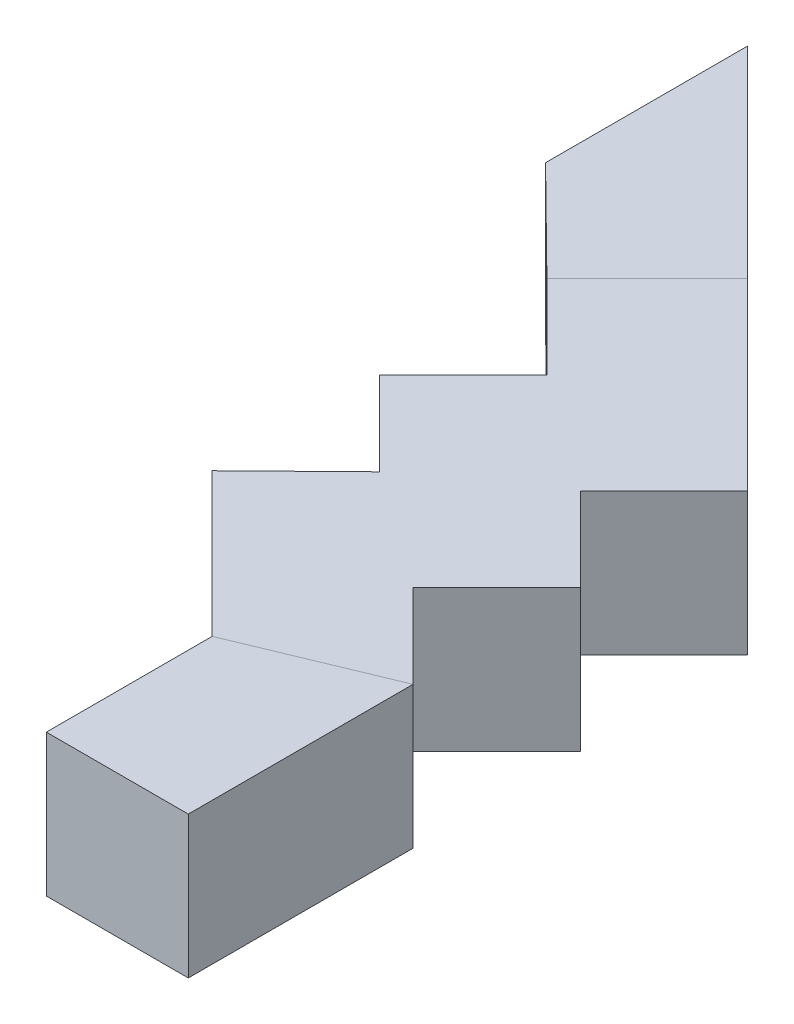
SolidWorks part; units mm, degrees
ref_plane "Front Plane" through (0, 0, 0) normal (0, 0, 1) x (1, 0, 0)
ref_plane "Top Plane" through (0, 0, 0) normal (0, 1, 0) x (1, 0, 0)
ref_plane "Right Plane" through (0, 0, 0) normal (1, 0, 0) x (0, 0, -1)
sketch "Sketch1" plane through (0, 0, 0) normal (0, 1, 0) x (1, 0, 0)
  line L0 (0, 0) -> (-1000, 0)
  line L1 (0, 0) -> (0, 600)
  line L2 (0, 600) -> (-1000, 600)
  line L3 (-1000, 0) -> (-2062.5184, -284.7009)
  line L4 (-2062.5184, -284.7009) -> (-3015.1464, -834.7009)
  line L5 (-1155.2914, 579.5555) -> (-2217.8098, 294.8545)
  line L6 (-1000, 600) -> (-1155.2914, 579.5555)
  line L7 (-3015.1464, -834.7009) -> (-3792.9638, -1612.5184)
  line L8 (-2217.8098, 294.8545) -> (-2362.5184, 234.9143)
  line L9 (-2362.5184, 234.9143) -> (-3315.1464, -315.0857)
  line L11 (-3439.4104, -410.4369) -> (-4217.2279, -1188.2543)
  line L12 (-3315.1464, -315.0857) -> (-3439.4104, -410.4369)
  line L26 (-8010.1917, -2800.7727) -> (-7010.1917, -2800.7727)
  line L27 (-8010.1917, -2800.7727) -> (-8010.1917, -3400.7727)
  line L28 (-8010.1917, -3400.7727) -> (-7010.1917, -3400.7727)
  line L29 (-7010.1917, -2800.7727) -> (-5947.6733, -2516.0718)
  line L30 (-5947.6733, -2516.0718) -> (-4995.0453, -1966.0718)
  line L31 (-6854.9003, -3380.3282) -> (-5792.3819, -3095.6273)
  line L32 (-7010.1917, -3400.7727) -> (-6854.9003, -3380.3282)
  line L33 (-4995.0453, -1966.0718) -> (-4217.2279, -1188.2543)
  line L34 (-5792.3819, -3095.6273) -> (-5647.6733, -3035.687)
  line L35 (-5647.6733, -3035.687) -> (-4695.0453, -2485.687)
  line L36 (-4570.7813, -2390.3359) -> (-3792.9638, -1612.5184)
  line L37 (-4695.0453, -2485.687) -> (-4570.7813, -2390.3359)
extrude "Boss-Extrude1" add sketch "Sketch1" against normal blind 600
sketch "Sketch7" plane through (0, 0, 0) normal (0, 0, 1) x (1, 0, 0)
  line L0 (-3015.1464, -400) -> (-3015.1464, 0)
  line L1 (-2062.5184, -600) -> (-2062.5184, 0) construction
  line L2 (-3015.1464, -400) -> (-2062.5184, -400)
  line L3 (-3015.1464, -600) -> (-3015.1464, 0) construction
  line L4 (-1000, -600) -> (-1000, 0)
  line L5 (-2062.5184, -400) -> (-1000, -600)
extrude "Cut-Extrude9" cut sketch "Sketch7" against normal through all and the other way through all
sketch "Sketch8" plane through (0, 0, 0) normal (0, 0, 1) x (1, 0, 0)
  line L0 (-1000, -600) -> (0, -600)
  line L1 (0, -600) -> (0, 0)
  line L2 (-1000, -600) -> (-1000, 0)
  line L5 (-4570.7813, -600) -> (-4570.7813, 0) construction
  line L6 (-4570.7813, -200) -> (-3015.1464, -400)
  line L7 (-4570.7813, -200) -> (-4695.0453, -200)
  line L8 (-4695.0453, -600) -> (-4695.0453, 0) construction
  line L9 (-4695.0453, -200) -> (-4695.0453, 0)
extrude "Cut-Extrude-Thin1" cut sketch "Sketch8" against normal through all thin thin type one direction wall 10
sketch "Sketch9" plane through (-1090.2227, 0, -1090.2227) normal (0.7071, 0, 0.7071) x (0.7071, 0, -0.7071)
  line L0 (-4922.2531, 0) -> (-4922.2531, -200)
  line L1 (-4922.2531, -600) -> (-4922.2531, 0) construction
  line L3 (-2722.2531, -400) -> (-2722.2531, 0)
  line L4 (-2722.2531, -400) -> (-2722.2531, 0) construction
sketch "Sketch14" plane through (0, -400, 0) normal (0, 1, 0) x (1, 0, 0)
  line L0 (-3015.1464, -834.7009) -> (-3439.4104, -410.4369)
  line L1 (-3015.1464, -834.7009) -> (-3015.1464, -141.8806)
  line L2 (-3015.1464, -834.7009) -> (-3015.1464, -141.8806) construction
  line L3 (-3015.1464, -834.7009) -> (-3015.1464, -141.8806) construction
  line L4 (-3315.1464, -315.0857) -> (-3015.1464, -141.8806)
  line L5 (-3439.4104, -410.4369) -> (-3315.1464, -315.0857)
extrude "Cut-Extrude40" cut sketch "Sketch14" along normal blind 400
sketch "Sketch17" plane through (-1090.2227, 0, -1090.2227) normal (0.7071, 0, 0.7071) x (0.7071, 0, -0.7071)
  line L0 (-2722.2531, -400) -> (-2722.2531, 0)
  line L1 (-4922.2531, -600) -> (-4922.2531, 0) construction
  line L2 (-2722.2531, -400) -> (-4922.2531, -200)
  line L3 (-4922.2531, -200) -> (-4922.2531, 0)
extrude "Cut-Extrude42" cut sketch "Sketch17" along normal through all and the other way through all flip side to cut
sketch "Sketch18" plane through (0, 0, 0) normal (0, 1, 0) x (1, 0, 0)
  line L0 (-4570.7813, -2390.3359) -> (-4995.0453, -1966.0718)
  line L1 (-4995.0453, -1966.0718) -> (-5947.6733, -2516.0718)
  line L2 (-5947.6733, -2516.0718) -> (-5792.3819, -3095.6273)
  line L3 (-5792.3819, -3095.6273) -> (-5647.6733, -3035.687) construction
  line L4 (-6854.9003, -3380.3282) -> (-5792.3819, -3095.6273) construction
  line L5 (-5792.3819, -3095.6273) -> (-5647.6733, -3035.687)
  line L6 (-5647.6733, -3035.687) -> (-4695.0453, -2485.687)
  line L7 (-4695.0453, -2485.687) -> (-4570.7813, -2390.3359)
extrude "Cut-Extrude43" cut sketch "Sketch18" against normal blind 200
sketch "Sketch19" plane through (385.8908, 0, 1440.1641) normal (0.2588, 0, 0.9659) x (0.9659, 0, -0.2588)
  line L0 (-6396.2185, -200) -> (-7496.2185, 0)
  line L1 (-6396.2185, -200) -> (-6396.2185, 0)
extrude "Cut-Extrude44" cut sketch "Sketch19" against normal through all and the other way through all
sketch "Sketch20" plane through (0, 0, 0) normal (0, 1, 0) x (1, 0, 0)
  line L0 (-7010.1917, -3400.7727) -> (-7010.1917, -2800.7727)
  line L1 (-7010.1917, -2800.7727) -> (-8010.1917, -2800.7727)
  line L2 (-7010.1917, -2800.7727) -> (-8010.1917, -2800.7727) construction
  line L3 (-8010.1917, -2800.7727) -> (-8010.1917, -3400.7727)
  line L4 (-8010.1917, -3400.7727) -> (-7010.1917, -3400.7727)
extrude "Cut-Extrude45" cut sketch "Sketch20" against normal blind 600
sketch "Sketch21" plane through (0, 0, 0) normal (0, 1, 0) x (1, 0, 0)
  line L0 (0, 0) -> (-10, 600)
  line L1 (-10, 600) -> (-990, 600)
  line L2 (-990, 600) -> (-1000, 0)
  line L4 (-1000, 0) -> (0, 0)
extrude "Cut-Extrude46" cut sketch "Sketch21" against normal blind 600
sketch "Sketch22" plane through (0, 0, 0) normal (0, 1, 0) x (1, 0, 0)
  line L0 (-7010.1917, -3400.7727) -> (-7610.1917, -3400.7727)
  line L1 (-7010.1917, -3400.7727) -> (-7010.1917, -2800.7727)
  line L2 (-7010.1917, -2800.7727) -> (-7010.1917, -1850.7727)
  line L3 (-7610.1917, -3400.7727) -> (-7610.1917, -2099.7727)
  line L4 (-7610.1917, -2099.7727) -> (-7010.1917, -1850.7727)
extrude "Boss-Extrude2" add sketch "Sketch22" against normal blind 600
sketch "Sketch23" plane through (0, 0, 0) normal (0, 1, 0) x (1, 0, 0)
  line L0 (-7010.1917, -1850.7727) -> (-7363.7451, -1497.2194)
  line L3 (-7610.1917, -2099.7727) -> (-8216.4721, -1493.4923)
  line L4 (-8216.4721, -1493.4923) -> (-7858.7198, -1143.666)
  line L5 (-7858.7198, -1143.666) -> (-8212.2732, -790.1126)
  line L6 (-7363.7451, -1497.2194) -> (-7010.1917, -1143.666)
  line L7 (-7010.1917, -1143.666) -> (-7363.7451, -790.1126)
  line L10 (-7858.7198, -436.5592) -> (-8212.2732, -790.1126)
  line L11 (-7858.7198, -436.5592) -> (-8212.2732, -83.0058)
  line L12 (-7363.7451, -790.1126) -> (-7010.1917, -436.5592)
  line L13 (-7010.1917, -436.5592) -> (-7369.5272, -77.2237)
  line L14 (-7369.5272, -77.2237) -> (-7793.7913, 347.0404)
  line L15 (-7858.7198, 270.5476) -> (-7793.7913, 347.0404)
  line L16 (-8212.2732, -83.0058) -> (-7858.7198, 270.5476)
  line L17 (-7610.1917, -2099.7727) -> (-7010.1917, -1850.7727)
extrude "Boss-Extrude3" add sketch "Sketch23" against normal blind 600
sketch "Sketch24" plane through (0, 0, 0) normal (0, 1, 0) x (1, 0, 0)
  line L0 (-7793.7913, 347.0404) -> (-8639.4431, 1192.6922)
  line L1 (-8212.2732, -83.0058) -> (-8639.4431, 338.3624)
  line L2 (-8639.4431, 338.3624) -> (-8639.4431, 1192.6922)
  line L3 (-8212.2732, -83.0058) -> (-7793.7913, 347.0404)
  line L4 (-8212.2732, -83.0058) -> (-7793.7913, 347.0404)
  dimension "D1" = 45
extrude "Boss-Extrude4" add sketch "Sketch24" against normal blind 600 separate body contours L1 L3 L0 L2
sketch "Sketch27" plane through (-4176.5499, 0, -4064.2397) normal (0.7167, 0, 0.6974) x (0.6974, 0, -0.7167)
  line L1 (-5786.77, 0) -> (-5186.7143, 0)
  line L2 (-5786.77, 0) -> (-5786.77, -600)
  line L3 (-5786.77, -600) -> (-5186.7143, -600)
  line L4 (-5186.7143, 0) -> (-5186.7143, -600)
extrude "Boss-Extrude5" add sketch "Sketch27" along normal up to next
sketch "Sketch29" plane through (0, 0, 0) normal (0, 1, 0) x (1, 0, 0)
  line L0 (-7610.1917, -2099.7727) -> (-7010.1917, -1850.7727)
  line L1 (-8212.2732, -83.0058) -> (-7788.0092, 341.2583)
  line L2 (-7010.1917, -436.5592) -> (-8639.4431, 1192.6922) construction
  line L3 (-8212.2732, -83.0058) -> (-7858.7198, -436.5592)
  line L4 (-7858.7198, -436.5592) -> (-8212.2732, -790.1126)
  line L5 (-8212.2732, -790.1126) -> (-7858.7198, -1143.666)
  line L6 (-7858.7198, -1143.666) -> (-8216.4721, -1493.4923)
  line L7 (-8216.4721, -1493.4923) -> (-7610.1917, -2099.7727)
  line L8 (-7010.1917, -1850.7727) -> (-7363.7451, -1497.2194)
  line L9 (-7363.7451, -1497.2194) -> (-7010.1917, -1143.666)
  line L10 (-7010.1917, -1143.666) -> (-7363.7451, -790.1126)
  line L11 (-7363.7451, -790.1126) -> (-7010.1917, -436.5592)
  line L12 (-7363.7451, -790.1126) -> (-7010.1917, -436.5592) construction
  line L13 (-7010.1917, -436.5592) -> (-7788.0092, 341.2583)
split line "Split Line1"
sketch "Sketch30" plane through (-3723.3754, 0, 3723.3754) normal (0.7071, 0, -0.7071) x (-0.7071, 0, -0.7071)
  line L0 (5748.2601, 0) -> (5748.2601, -600)
  line L1 (4648.2601, -600) -> (6952.3696, -600) construction
split line "Split Line2"
sketch "Sketch31" plane through (-222.2787, 0, -829.5555) normal (-0.2588, 0, -0.9659) x (-0.9659, 0, 0.2588)
  line L0 (1905.1563, -400) -> (1905.1563, -600)
  line L1 (965.9258, -600) -> (2065.9258, -600) construction
split line "Split Line3"
sketch "Sketch39" plane through (0, 0, 0) normal (0, 1, 0) x (1, 0, 0)
  line L0 (-7010.1917, -2800.7727) -> (-7610.1917, -2800.7727)
  line L1 (-7610.1917, -2099.7727) -> (-7610.1917, -3400.7727) construction
ref_plane "Plane2" through (-7010.1917, 0, 0) normal (1, 0, 0) x (0, 0, -1)
sketch "Sketch41" plane through (-7010.1917, 0, 0) normal (1, 0, 0) x (0, 0, -1)
  line L1 (-4395.6011, 900.6876) -> (1548.9916, 900.6876)
  line L2 (-4395.6011, 900.6876) -> (-4395.6011, -944.9527)
  line L3 (-4395.6011, -944.9527) -> (1548.9916, -944.9527)
  line L4 (1548.9916, 900.6876) -> (1548.9916, -944.9527)
extrude "Cut-Extrude49" cut sketch "Sketch41" along normal blind 10020
ref_plane "Plane3" through (0, 0, 2800.7727) normal (0, 0, 1) x (1, 0, 0)
sketch "Sketch42" plane through (0, 0, 2800.7727) normal (0, 0, 1) x (1, 0, 0)
  line L1 (-6414.9989, 710.8912) -> (-9646.0999, 710.8912)
  line L2 (-6414.9989, 710.8912) -> (-6414.9989, -1532.537)
  line L3 (-6414.9989, -1532.537) -> (-9646.0999, -1532.537)
  line L4 (-9646.0999, 710.8912) -> (-9646.0999, -1532.537)
extrude "Cut-Extrude50" cut sketch "Sketch42" along normal blind 10020
